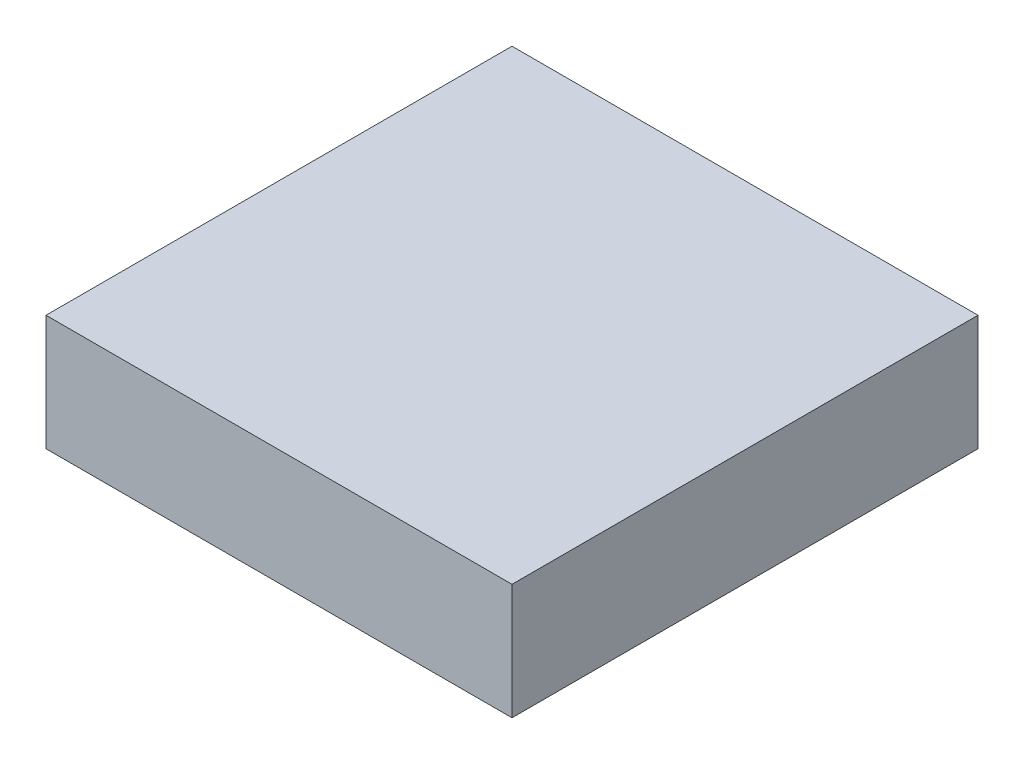
SolidWorks part; units mm, degrees
ref_plane "Front Plane" through (0, 0, 0) normal (0, 0, 1) x (1, 0, 0)
ref_plane "Top Plane" through (0, 0, 0) normal (0, 1, 0) x (1, 0, 0)
ref_plane "Right Plane" through (0, 0, 0) normal (1, 0, 0) x (0, 0, -1)
sketch "Sketch2" plane through (0, 0, 0) normal (0, 1, 0) x (1, 0, 0)
  line L1 (-2, 2) -> (2, 2)
  line L2 (-2, 2) -> (-2, -2)
  line L3 (-2, -2) -> (2, -2)
  line L4 (2, 2) -> (2, -2)
  line L5 (-2, 2) -> (2, -2) construction
  line L6 (-2, -2) -> (2, 2) construction
  point P0 (0, 0)
  dimension "D1" = 4
  dimension "D2" = 4
extrude "Boss-Extrude1" add sketch "Sketch2" along normal blind 0.9925
sketch "Sketch3" plane through (0, 0, 0) normal (0, -1, 0) x (1, 0, 0)
  line L0 (0, 2) -> (0, -2) construction
  line L1 (-2, 2) -> (2, 2) construction
  line L2 (2, -2) -> (-2, -2) construction
  line L3 (-0.625, 1.88) -> (-0.625, 1.53)
  line L4 (-2, -2) -> (-2, 2) construction
  line L5 (-2, 0) -> (2, 0) construction
  line L6 (2, 2) -> (2, -2) construction
  line L7 (-0.375, 1.88) -> (-0.125, 1.88)
  line L8 (-0.375, 1.88) -> (-0.375, 1.53)
  line L9 (-0.375, 1.53) -> (-0.125, 1.53)
  line L10 (-0.125, 1.88) -> (-0.125, 1.53)
  line L11 (-0.375, 1.88) -> (-0.125, 1.53) construction
  line L12 (-0.375, 1.53) -> (-0.125, 1.88) construction
  line L13 (-0.875, 1.53) -> (-0.625, 1.53)
  line L14 (-0.875, 1.88) -> (-0.875, 1.53)
  line L15 (-0.875, 1.88) -> (-0.625, 1.88)
  line L16 (-1.125, 1.88) -> (-1.125, 1.53)
  line L17 (-1.375, 1.53) -> (-1.125, 1.53)
  line L18 (-1.375, 1.88) -> (-1.375, 1.53)
  line L19 (-1.375, 1.88) -> (-1.125, 1.88)
  line L20 (0.375, 1.88) -> (0.375, 1.53)
  line L21 (0.125, 1.53) -> (0.375, 1.53)
  line L22 (0.125, 1.88) -> (0.125, 1.53)
  line L23 (0.125, 1.88) -> (0.375, 1.88)
  line L24 (0.875, 1.88) -> (0.875, 1.53)
  line L25 (0.625, 1.53) -> (0.875, 1.53)
  line L26 (0.625, 1.88) -> (0.625, 1.53)
  line L27 (0.625, 1.88) -> (0.875, 1.88)
  line L28 (1.375, 1.88) -> (1.375, 1.53)
  line L29 (1.125, 1.53) -> (1.375, 1.53)
  line L30 (1.125, 1.88) -> (1.125, 1.53)
  line L31 (1.125, 1.88) -> (1.375, 1.88)
  line L32 (-2, 2) -> (0, 0) construction
  line L33 (-0.375, -1.53) -> (-0.125, -1.88) construction
  line L34 (-0.375, -1.88) -> (-0.125, -1.53) construction
  line L35 (1.125, -1.88) -> (1.375, -1.88)
  line L36 (-1.53, 0.375) -> (-1.88, 0.125) construction
  line L37 (-1.88, 0.375) -> (-1.53, 0.125) construction
  line L38 (-1.88, 1.375) -> (-1.88, 1.125)
  line L39 (-1.88, 1.375) -> (-1.53, 1.375)
  line L40 (-1.53, 1.375) -> (-1.53, 1.125)
  line L41 (-1.88, 1.125) -> (-1.53, 1.125)
  line L42 (-1.88, 0.875) -> (-1.88, 0.625)
  line L43 (-1.88, 0.875) -> (-1.53, 0.875)
  line L44 (-1.53, 0.875) -> (-1.53, 0.625)
  line L45 (-1.88, 0.125) -> (-1.53, 0.125)
  line L46 (-1.53, 0.375) -> (-1.53, 0.125)
  line L47 (-1.88, 0.375) -> (-1.53, 0.375)
  line L48 (-1.88, 0.375) -> (-1.88, 0.125)
  line L49 (-1.88, 0.625) -> (-1.53, 0.625)
  line L50 (1.125, -1.88) -> (1.125, -1.53)
  line L51 (1.125, -1.53) -> (1.375, -1.53)
  line L52 (1.375, -1.88) -> (1.375, -1.53)
  line L53 (0.625, -1.88) -> (0.875, -1.88)
  line L54 (0.625, -1.88) -> (0.625, -1.53)
  line L55 (0.625, -1.53) -> (0.875, -1.53)
  line L56 (0.875, -1.88) -> (0.875, -1.53)
  line L57 (0.125, -1.88) -> (0.375, -1.88)
  line L58 (0.125, -1.88) -> (0.125, -1.53)
  line L59 (0.125, -1.53) -> (0.375, -1.53)
  line L60 (0.375, -1.88) -> (0.375, -1.53)
  line L61 (-1.375, -1.88) -> (-1.125, -1.88)
  line L62 (-1.375, -1.88) -> (-1.375, -1.53)
  line L63 (-1.375, -1.53) -> (-1.125, -1.53)
  line L64 (-1.125, -1.88) -> (-1.125, -1.53)
  line L65 (-0.875, -1.88) -> (-0.625, -1.88)
  line L66 (-0.875, -1.88) -> (-0.875, -1.53)
  line L67 (-0.875, -1.53) -> (-0.625, -1.53)
  line L68 (-0.125, -1.88) -> (-0.125, -1.53)
  line L69 (-0.375, -1.53) -> (-0.125, -1.53)
  line L70 (-0.375, -1.88) -> (-0.375, -1.53)
  line L71 (-0.375, -1.88) -> (-0.125, -1.88)
  line L72 (-0.625, -1.88) -> (-0.625, -1.53)
  line L73 (-2, -2) -> (0, 0) construction
  line L74 (-1.88, -0.375) -> (-1.53, -0.125) construction
  line L75 (-1.53, -0.375) -> (-1.88, -0.125) construction
  line L76 (-1.88, -0.625) -> (-1.53, -0.625)
  line L77 (-1.88, -0.375) -> (-1.88, -0.125)
  line L78 (-1.88, -0.375) -> (-1.53, -0.375)
  line L79 (-1.53, -0.375) -> (-1.53, -0.125)
  line L80 (-1.88, -0.125) -> (-1.53, -0.125)
  line L81 (-1.53, -0.875) -> (-1.53, -0.625)
  line L82 (-1.88, -0.875) -> (-1.53, -0.875)
  line L83 (-1.88, -0.875) -> (-1.88, -0.625)
  line L84 (-1.88, -1.125) -> (-1.53, -1.125)
  line L85 (-1.53, -1.375) -> (-1.53, -1.125)
  line L86 (-1.88, -1.375) -> (-1.53, -1.375)
  line L87 (-1.88, -1.375) -> (-1.88, -1.125)
  line L88 (1.53, -0.375) -> (1.88, -0.125) construction
  line L89 (1.88, -0.375) -> (1.53, -0.125) construction
  line L90 (1.88, 0.375) -> (1.53, 0.125) construction
  line L91 (1.53, 0.375) -> (1.88, 0.125) construction
  line L92 (1.88, -1.375) -> (1.88, -1.125)
  line L93 (1.88, -1.375) -> (1.53, -1.375)
  line L94 (1.53, -1.375) -> (1.53, -1.125)
  line L95 (1.88, -1.125) -> (1.53, -1.125)
  line L96 (1.88, -0.875) -> (1.88, -0.625)
  line L97 (1.88, -0.875) -> (1.53, -0.875)
  line L98 (1.53, -0.875) -> (1.53, -0.625)
  line L99 (1.88, -0.125) -> (1.53, -0.125)
  line L100 (1.53, -0.375) -> (1.53, -0.125)
  line L101 (1.88, -0.375) -> (1.53, -0.375)
  line L102 (1.88, -0.375) -> (1.88, -0.125)
  line L103 (1.88, -0.625) -> (1.53, -0.625)
  line L104 (1.88, 0.625) -> (1.53, 0.625)
  line L105 (1.88, 0.375) -> (1.88, 0.125)
  line L106 (1.88, 0.375) -> (1.53, 0.375)
  line L107 (1.53, 0.375) -> (1.53, 0.125)
  line L108 (1.88, 0.125) -> (1.53, 0.125)
  line L109 (1.53, 0.875) -> (1.53, 0.625)
  line L110 (1.88, 0.875) -> (1.53, 0.875)
  line L111 (1.88, 0.875) -> (1.88, 0.625)
  line L112 (1.88, 1.125) -> (1.53, 1.125)
  line L113 (1.53, 1.375) -> (1.53, 1.125)
  line L114 (1.88, 1.375) -> (1.53, 1.375)
  line L115 (1.88, 1.375) -> (1.88, 1.125)
  point P12 (-0.25, 1.705)
  point P53 (-1.705, 0.25)
  point P78 (-0.25, -1.705)
  point P94 (-1.705, -0.25)
  point P119 (1.705, -0.25)
  point P120 (1.705, 0.25)
  dimension "D1" = 0.25
  dimension "D2" = 0.12
  dimension "D3" = 0.35
  dimension "D4" = 0.25
  dimension "D5" = 3
  dimension "D6" = 4
extrude "Boss-Extrude2" add sketch "Sketch3" along normal blind 0.075
